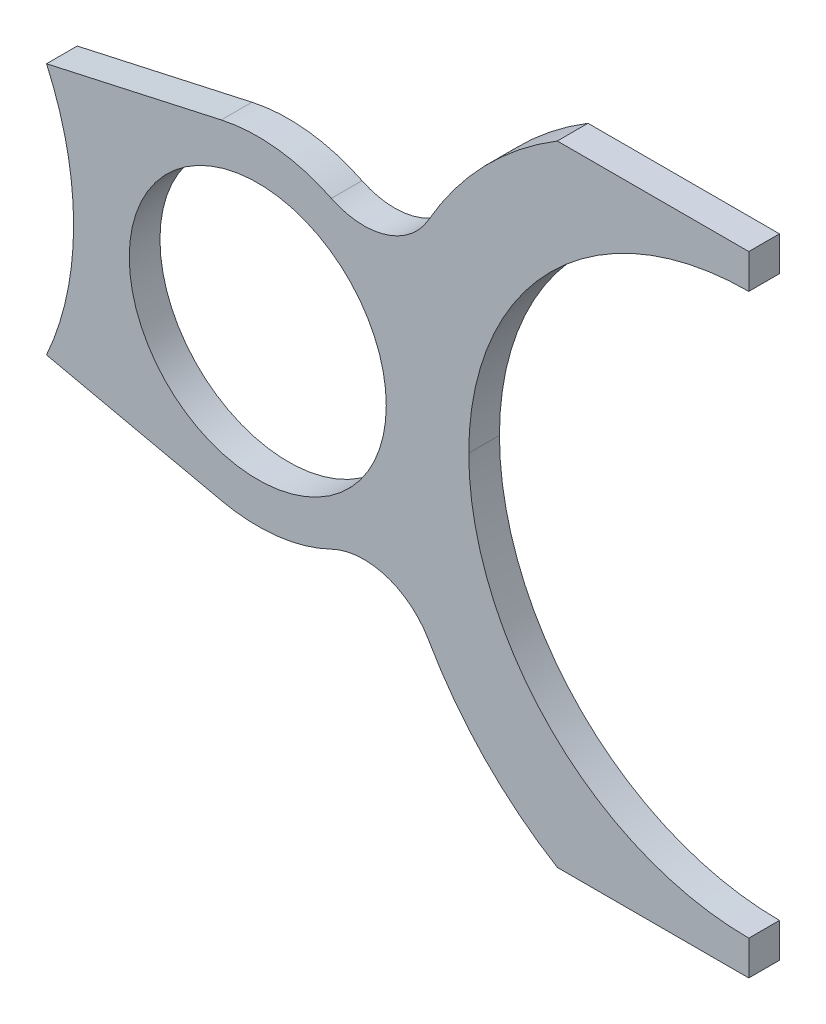
SolidWorks part; units mm, degrees
ref_plane "Front Plane" through (0, 0, 0) normal (0, 0, 1) x (1, 0, 0)
ref_plane "Top Plane" through (0, 0, 0) normal (0, 1, 0) x (1, 0, 0)
ref_plane "Right Plane" through (0, 0, 0) normal (1, 0, 0) x (0, 0, -1)
sketch "Model" plane through (0, 0, 0) normal (0, 0, 1) x (1, 0, 0)
  line L0 (74.448, 2.2499) -> (74.448, 4.5001)
  line L1 (74.448, 4.5001) -> (61.9682, 4.5)
  line L2 (40.0694, -5.2602) -> (28.6821, -7.7823)
  line L3 (28.6821, -24.2177) -> (40.0694, -26.7398)
  line L4 (61.9682, -36.5) -> (74.448, -36.5001)
  line L5 (74.448, -36.5001) -> (74.448, -34.2499)
  circle A0 centre (42.448, -16) radius 8.375
  arc A1 (74.448, 2.2499) -> (56.198, -16.0001) centre (74.448, -16.0001) ccw
  arc A2 (61.9682, 4.5) -> (53.5885, -4.1308) centre (74.448, -16.0001) ccw
  arc A3 (47.2448, -6.1009) -> (53.5885, -4.1308) centre (49.3642, -1.7271) ccw
  arc A4 (47.2448, -6.1009) -> (40.0694, -5.2602) centre (42.448, -16) ccw
  arc A5 (30.4483, -16) -> (28.6821, -7.7823) centre (10.4483, -15.9998) ccw
  arc A6 (28.6821, -24.2177) -> (30.4483, -16) centre (10.4483, -16.0002) ccw
  arc A7 (40.0694, -26.7398) -> (47.2448, -25.8991) centre (42.448, -16) ccw
  arc A8 (53.5885, -27.8692) -> (47.2448, -25.8991) centre (49.3642, -30.2729) ccw
  arc A9 (53.5885, -27.8692) -> (61.9682, -36.5) centre (74.448, -15.9999) ccw
  arc A10 (56.198, -16.0001) -> (74.448, -34.2499) centre (74.448, -15.9999) ccw
extrude "Boss-Extrude1" add sketch "Model" along normal blind 2
